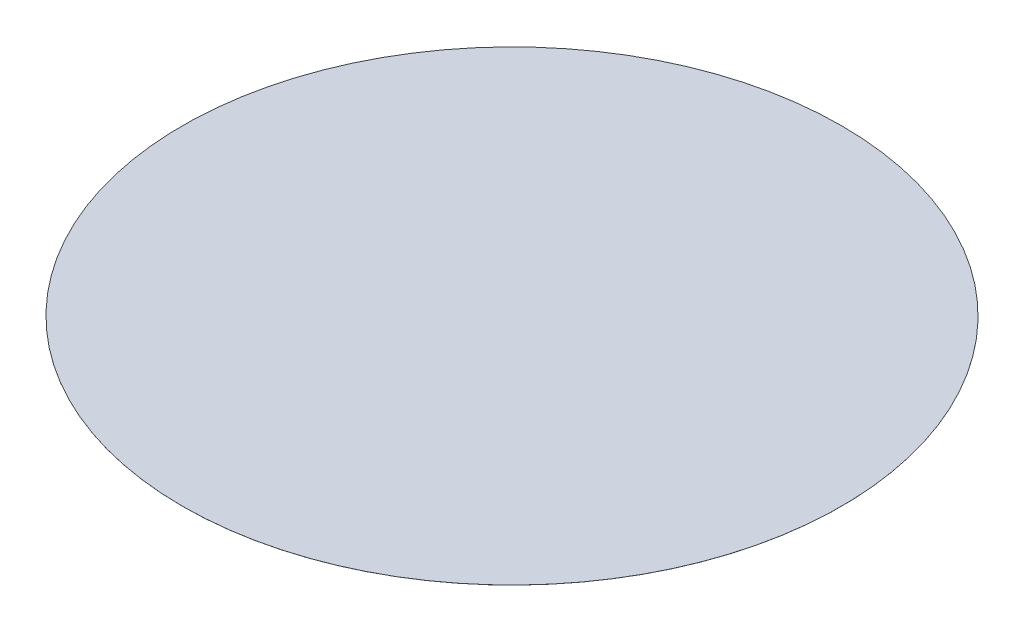
SolidWorks part; units mm, degrees
ref_plane "Front Plane" through (0, 0, 0) normal (0, 0, 1) x (1, 0, 0)
ref_plane "Top Plane" through (0, 0, 0) normal (0, 1, 0) x (1, 0, 0)
ref_plane "Right Plane" through (0, 0, 0) normal (1, 0, 0) x (0, 0, -1)
sketch "Sketch1" plane through (0, 0, 0) normal (0, 1, 0) x (1, 0, 0)
  circle A0 centre (0, 0) radius 10.65
  dimension "D1" = 21.3
extrude "Boss-Extrude1" add sketch "Sketch1" along normal blind 15.5
sketch "Sketch4" plane through (0, 15.5, 0) normal (0, 1, 0) x (1, 0, 0)
  circle A0 centre (0, 0) radius 63.5
  dimension "D1" = 127
extrude "Boss-Extrude4" add sketch "Sketch4" along normal blind 0.01 from offset 1
